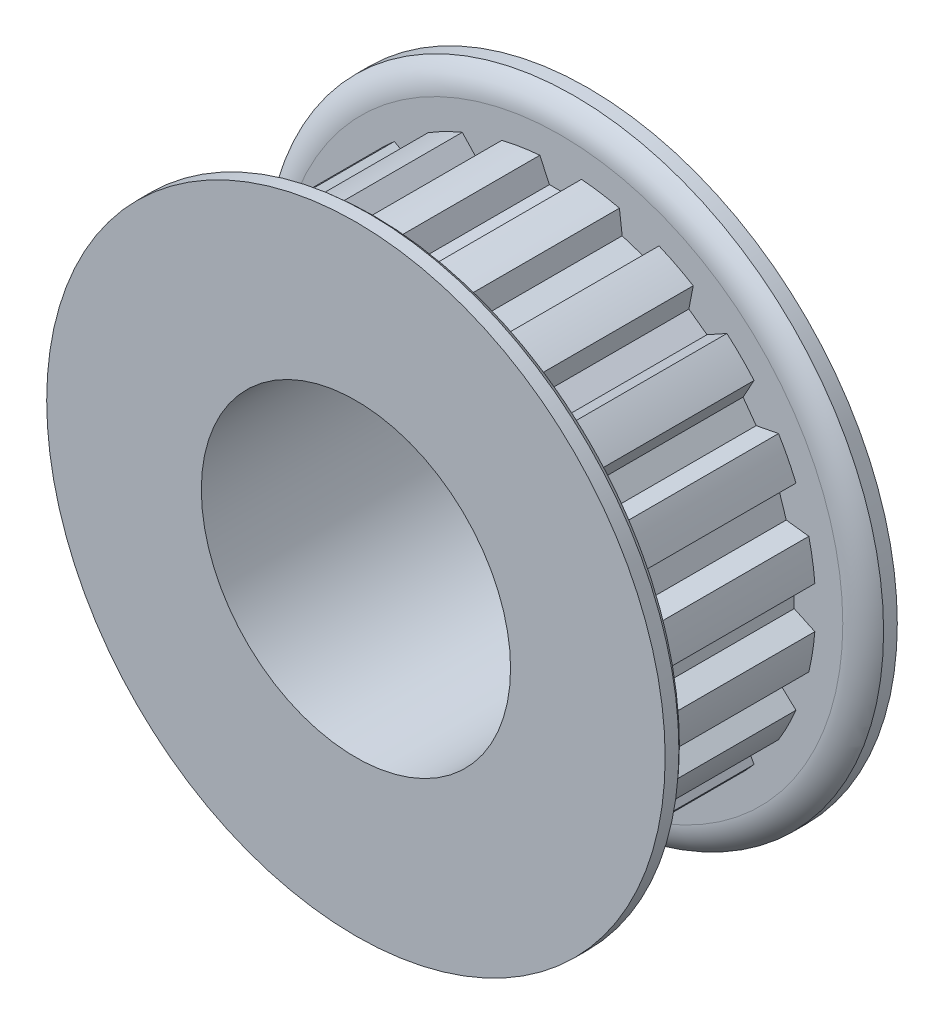
SolidWorks part; units mm, degrees
ref_plane "Front Plane" through (0, 0, 0) normal (0, 0, 1) x (1, 0, 0)
ref_plane "Top Plane" through (0, 0, 0) normal (0, 1, 0) x (1, 0, 0)
ref_plane "Right Plane" through (0, 0, 0) normal (1, 0, 0) x (0, 0, -1)
sketch "Sketch1" plane through (0, 0, 0) normal (0, 0, 1) x (1, 0, 0)
  line L0 (-1.2827, 15.6591) -> (-0.6905, 14.3891)
  line L1 (-0.6905, 14.3891) -> (0.6905, 14.3891)
  line L2 (0.6905, 14.3891) -> (1.2827, 15.6591)
  line L3 (-1.2827, 15.6591) -> (1.2827, 15.6591)
  line L4 (0, 0) -> (0, 14.3891) construction
  line L5 (0, 14.3891) -> (0, 16.6751) construction
  circle A0 centre (0, 0) radius 16.1671 construction
  circle A1 centre (0, 0) radius 19.05 construction
  circle A2 centre (0, 0) radius 15.7115 construction
  point P6 (0, 15.6591)
  point P11 (0, 16.1671)
  point P13 (0, 19.05)
  point P14 (0, 15.7115)
  dimension "D1" = 1.016
  dimension "PD" = 32.3342
  dimension "D2" = 0.508
  dimension "OD" = 38.1
  dimension "b" = 50
  dimension "bt" = 2.5654
  dimension "ht" = 1.27
  dimension "hs" = 2.286
sketch "Sketch2" plane through (0, 0, 0) normal (1, 0, 0) x (0, 0, -1)
  line L0 (-3.1877, 3.175) -> (11.1125, 3.175)
  line L3 (-3.1877, 11.8999) -> (-3.1877, 19.05)
  line L4 (-3.1877, 19.05) -> (-1.4986, 19.05) construction
  line L5 (-1.4986, 19.05) -> (-1.4986, 15.7115) construction
  line L6 (-1.4986, 15.7115) -> (9.4234, 15.7115)
  line L7 (9.4234, 15.7115) -> (9.4234, 19.05) construction
  line L8 (9.4234, 19.05) -> (11.1125, 19.05) construction
  line L9 (11.1125, 19.05) -> (11.1125, 3.175)
  line L10 (-11.1125, 0) -> (11.1125, 0) construction
  line L11 (-3.1877, 11.8999) -> (-3.1877, 3.175)
  line L13 (-3.1877, 19.05) -> (-2.3431, 19.05)
  line L14 (-1.4986, 17.3808) -> (-1.4986, 15.7115)
  line L15 (9.4234, 15.7115) -> (9.4234, 17.3808)
  line L16 (10.268, 19.05) -> (11.1125, 19.05)
  arc A0 (-1.4986, 17.3808) -> (-2.3431, 19.05) centre (-3.5705, 17.3808) ccw
  arc A1 (9.4234, 17.3808) -> (10.268, 19.05) centre (11.4953, 17.3808) cw
  point P12 (-1.4986, 17.3808)
  point P14 (-2.3431, 19.05)
  point P20 (9.4234, 17.3808)
  point P21 (10.268, 19.05)
  point P25 (9.4234, 0)
  point P26 (-1.4986, 0)
  dimension "D1" = 8.7249
  dimension "OA" = 22.225
  dimension "Bore" = 6.35
  dimension "Outside Width" = 14.3002
  dimension "Inside Width" = 10.922
revolve "Revolve1" add sketch "Sketch2" angle 360 mid plane about L10
sketch "Sketch3" plane through (0, 0, 0) normal (0, 0, 1) x (1, 0, 0)
  line L0 (-0.6905, 14.3891) -> (0.6905, 14.3891) construction
  line L1 (0.6905, 14.3891) -> (1.2827, 15.6591) construction
  line L2 (-1.2827, 15.6591) -> (-0.6905, 14.3891) construction
  line L3 (-0.6905, 14.3891) -> (0.6905, 14.3891)
  line L4 (0.6905, 14.3891) -> (1.2827, 15.6591)
  line L5 (-1.2827, 15.6591) -> (-0.6905, 14.3891)
  circle A0 centre (0, 0) radius 15.7115 construction
  arc A1 (1.2827, 15.6591) -> (-1.2827, 15.6591) centre (0, 0) ccw
extrude "Cut-Extrude1" cut sketch "Sketch3" against normal up to vertex (9.4234 mm away) from vertex at 1.4986 starting at point (0, 15.7115, 1.4986)
pattern_circular "CirPattern1" count 20 over 360 about axis through (0, 0, 0) along (0, 0, 1) of "Cut-Extrude1"
sketch "Sketch4" plane through (0, 0, 3.1877) normal (0, 0, 1) x (1, 0, 0)
  circle A0 centre (0, 0) radius 9.525
  dimension "D1" = 19.05
extrude "Cut-Extrude2" cut sketch "Sketch4" against normal through all
